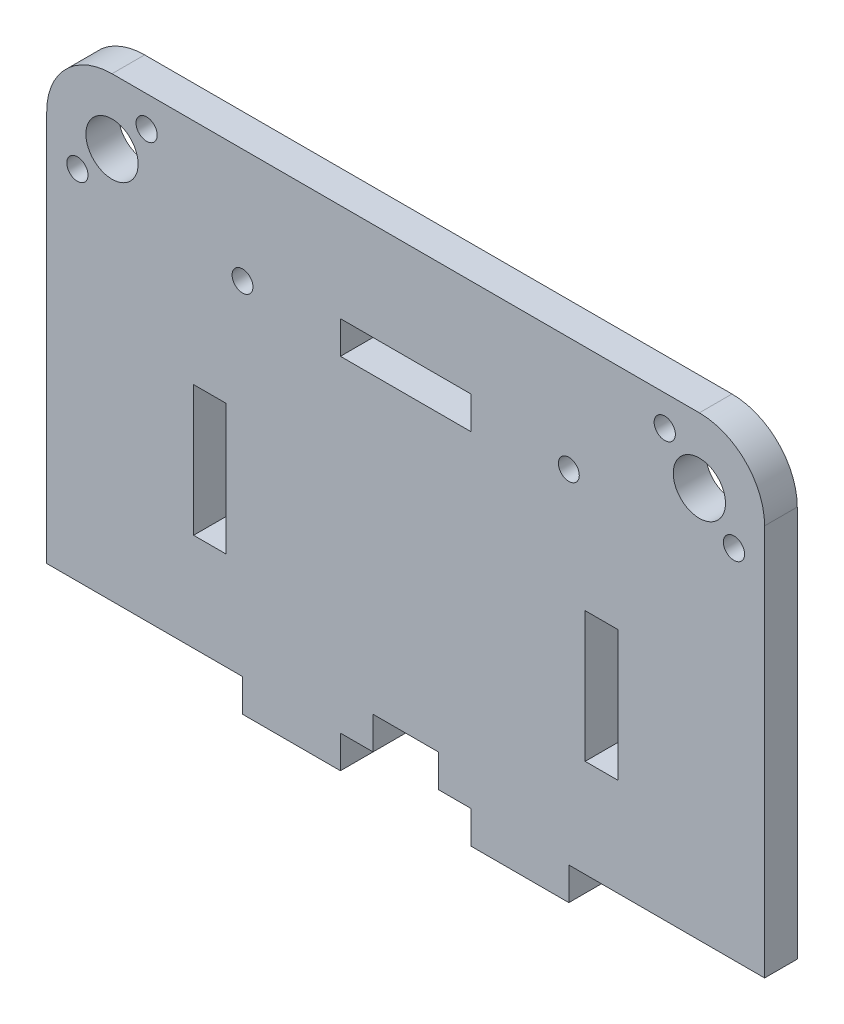
SolidWorks part; units mm, degrees
ref_plane "Plan de face" through (0, 0, 0) normal (0, 0, 1) x (1, 0, 0)
ref_plane "Plan de dessus" through (0, 0, 0) normal (0, 1, 0) x (1, 0, 0)
ref_plane "Plan de droite" through (0, 0, 0) normal (1, 0, 0) x (0, 0, -1)
sketch "Esquisse1" plane through (0, 0, 0) normal (0, 0, 1) x (1, 0, 0)
  line L0 (0, 35) -> (0, -35) construction
  line L1 (-55, 35) -> (55, 35)
  line L2 (-55, 35) -> (-55, -35)
  line L3 (-55, -35) -> (-25, -35)
  line L4 (55, 35) -> (55, -35)
  line L5 (-55, 0) -> (55, 0) construction
  line L6 (-25, -35) -> (-25, -40)
  line L7 (-25, -40) -> (-10, -40)
  line L8 (-10, -40) -> (-10, -35)
  line L9 (10, -35) -> (10, -40)
  line L10 (10, -40) -> (25, -40)
  line L11 (25, -40) -> (25, -35)
  line L12 (-10, -35) -> (-5, -35)
  line L13 (25, -35) -> (55, -35)
  line L14 (-32.5, -10) -> (-27.5, -10) construction
  line L15 (-32.5, 0) -> (-27.5, 0)
  line L16 (-32.5, 0) -> (-32.5, -20)
  line L17 (-32.5, -20) -> (-27.5, -20)
  line L18 (-27.5, 0) -> (-27.5, -20)
  line L19 (27.5, 0) -> (32.5, 0)
  line L20 (27.5, 0) -> (27.5, -20)
  line L21 (27.5, -20) -> (32.5, -20)
  line L22 (32.5, 0) -> (32.5, -20)
  line L23 (5, -35) -> (5, -30)
  line L24 (-10, 20) -> (10, 20)
  line L25 (-10, 20) -> (-10, 15)
  line L26 (-10, 15) -> (10, 15)
  line L27 (10, 20) -> (10, 15)
  line L28 (-4.7305, 15) -> (-4.7305, -35) construction
  line L29 (-4.7305, -10) -> (16.2582, -10) construction
  line L30 (5, -30) -> (-5, -30)
  line L31 (-5, -30) -> (-5, -35)
  line L32 (5, -35) -> (10, -35)
  line L33 (10, 17.5) -> (16.742, 17.5) construction
  circle A0 centre (-25, 17.5) radius 1.6
  circle A1 centre (25, 17.5) radius 1.6
  point P8 (0, 0)
  point P11 (0, 0)
  point P45 (0, 0)
  point P48 (0, 0)
  dimension "D19" = 3.2
  dimension "D21" = 3.2
  dimension "D1" = 70
  dimension "D2" = 110
  dimension "D3" = 20
  dimension "D4" = 10
  dimension "D5" = 15
  dimension "D6" = 15
  dimension "D7" = 5
  dimension "D8" = 5
  dimension "D9" = 5
  dimension "D10" = 55
  dimension "D11" = 20
  dimension "D12" = 27.5
  dimension "D13" = 5
  dimension "D14" = 50
  dimension "D15" = 5
  dimension "D16" = 10
  dimension "D17" = 5
  dimension "D18" = 25
  dimension "D20" = 25
extrude "Boss.-Extru.1" add sketch "Esquisse1" along normal blind 5
fillet "Congé1" radius 10 2 edges at (-55, 35, 2.5) (55, 35, 2.5)
sketch "Esquisse2" plane through (0, 0, 0) normal (0, 0, -1) x (-1, 0, 0)
  line L0 (-50.3033, 19.6967) -> (-34.4319, 35.5681) construction
  line L1 (-34.4319, 35.5681) -> (-50.3033, 19.6967) construction
  line L2 (-50.3033, 19.6967) -> (-28.038, 19.6967) construction
  line L3 (0, 35) -> (0, -16.4032) construction
  line L4 (-45, 35) -> (45, 35) construction
  line L5 (-55, -35) -> (-55, 25) construction
  circle A0 centre (-45, 25) radius 4
  circle A1 centre (-50.3033, 19.6967) radius 1.625
  circle A2 centre (-39.6967, 30.3033) radius 1.625
  dimension "D1" = 8
  dimension "D2" = 3.25
  dimension "D3" = 3.25
  dimension "D4" = 15
  dimension "D5" = 7.5
  dimension "D6" = 45
  dimension "D7" = 45
  dimension "D8" = 10
  dimension "D9" = 10
extrude "Enlèv. mat.-Extru.1" cut sketch "Esquisse2" against normal blind 10
ref_plane "Plan1" through (0, 0, 0) normal (1, 0, 0) x (0, 0, -1)
mirror "Symétrie1" about plane through (0, 0, 0) normal (1, 0, 0) of "Enlèv. mat.-Extru.1"
equation "\"D4@Esquisse1\"=\"D3@Esquisse1\"/2"
equation "\"D6@Esquisse1\"=\"D5@Esquisse1\""
equation "\"D8@Esquisse1\"=\"D7@Esquisse1\""
equation "\"D9@Esquisse1\"=\"D7@Esquisse1\""
equation "\"D12@Esquisse1\"=\"D10@Esquisse1\"/2"
equation "\"D13@Esquisse1\"=\"D7@Esquisse1\""
equation "\"D15@Esquisse1\"=\"D7@Esquisse1\""
equation "\"D17@Esquisse1\"=\"D16@Esquisse1\"/2"
equation "\"D3@Esquisse2\"=\"D2@Esquisse2\""
equation "\"D5@Esquisse2\"=\"D4@Esquisse2\"/2"
equation "\"D9@Esquisse2\"=\"D8@Esquisse2\""
